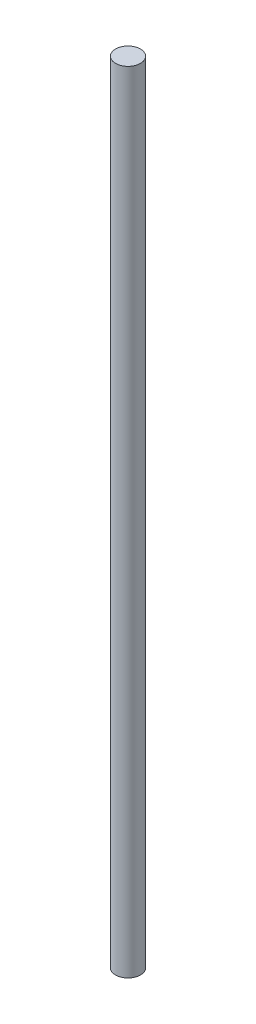
SolidWorks part; units mm, degrees
ref_plane "Front Plane" through (0, 0, 0) normal (0, 0, 1) x (1, 0, 0)
ref_plane "Top Plane" through (0, 0, 0) normal (0, 1, 0) x (1, 0, 0)
ref_plane "Right Plane" through (0, 0, 0) normal (1, 0, 0) x (0, 0, -1)
sketch "Sketch1" plane through (0, 0, 0) normal (0, 1, 0) x (1, 0, 0)
  circle A0 centre (0, 0) radius 1.5
  dimension "D1" = 3
extrude "Boss-Extrude1" add sketch "Sketch1" along normal blind 95
